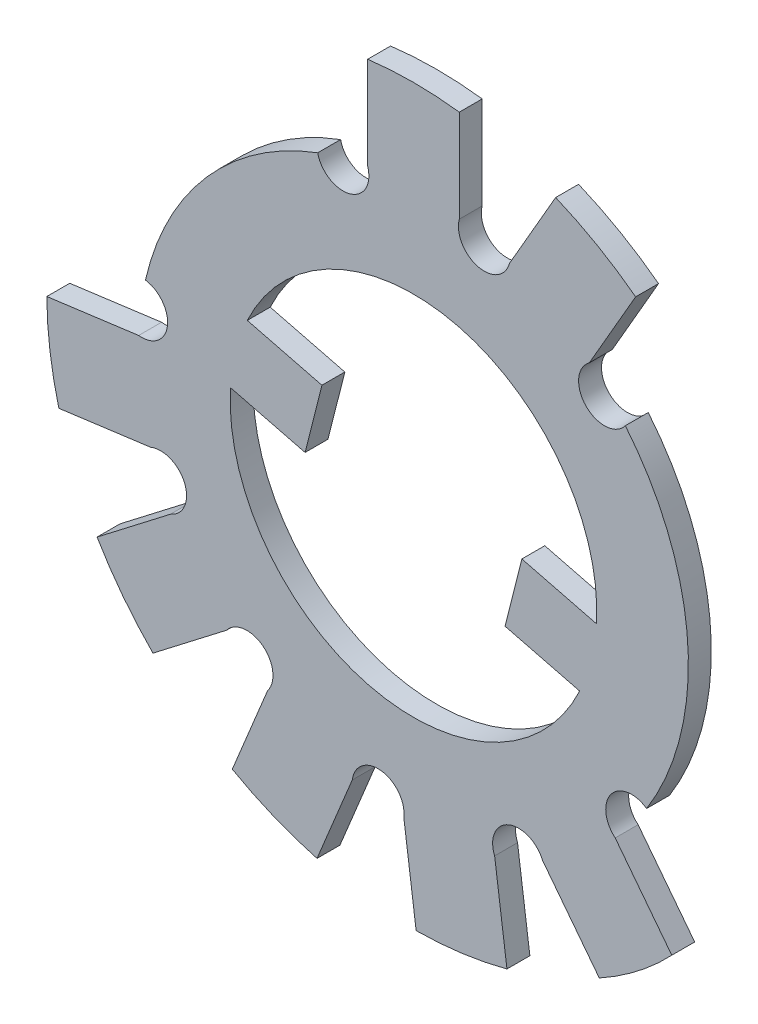
SolidWorks part; units mm, degrees
ref_plane "Face" through (0, 0, 0) normal (0, 0, 1) x (1, 0, 0)
ref_plane "Dessus" through (0, 0, 0) normal (0, 1, 0) x (1, 0, 0)
ref_plane "Droite" through (0, 0, 0) normal (1, 0, 0) x (0, 0, -1)
sketch "Esquisse1" plane through (0, 0, 0) normal (0, 0, 1) x (1, 0, 0)
  line L0 (0, 0) -> (0, 17.0651) construction
  line L1 (0, 0) -> (1.3955, 1.3955) construction
  line L2 (1.9991, 15.8746) -> (1.9991, 11.8301)
  line L3 (0, 0) -> (12.3609, 21.4097) construction
  line L4 (-1.9991, 11.8323) -> (-1.9991, 15.8746)
  line L5 (4.1862, 11.2489) -> (6.2054, 14.7508)
  line L6 (9.6952, 12.7421) -> (7.6749, 9.2384)
  line L7 (-11.4682, -3.5253) -> (-15.4754, -4.057)
  line L8 (-16.0013, -0.0935) -> (-11.992, 0.4385)
  line L9 (-13.8069, -8.0883) -> (-10.6019, -5.6214)
  line L10 (-8.1649, -8.7911) -> (-11.3682, -11.2567)
  line L11 (-7.9063, -13.9119) -> (-6.366, -10.1722)
  line L12 (-2.6699, -11.697) -> (-4.2094, -15.4347)
  line L13 (0.1166, -16.0012) -> (-0.4212, -11.9926)
  line L14 (3.5418, -11.4632) -> (4.0793, -15.4696)
  line L15 (8.1082, -13.7953) -> (5.6366, -10.5938)
  line L16 (8.8028, -8.1523) -> (11.273, -11.352)
  line L17 (7.9862, -0.4691) -> (4.7303, 0.3529)
  line L18 (0.025, -0.0227) -> (9.7847, -12.6956) construction
  line L19 (-0.0128, -0.0017) -> (-15.8627, -2.0918) construction
  line L20 (3.9959, -2.5559) -> (7.2519, -3.3778)
  line L21 (-7.2519, 3.3778) -> (-3.9959, 2.5559)
  line L22 (-3.9959, 2.5559) -> (-4.7303, -0.3529)
  line L23 (-4.7303, -0.3529) -> (-7.9862, 0.4691)
  line L24 (4.7303, 0.3529) -> (3.9959, -2.5559)
  arc A0 (-4.1799, 11.2485) -> (-11.6971, 2.679) centre (0, 0) ccw
  arc A1 (7.9862, -0.4691) -> (-7.2519, 3.3778) centre (0, 0) ccw
  arc A2 (1.9991, 15.8746) -> (-1.9991, 15.8746) centre (0, 0) ccw
  arc A3 (9.6952, 12.7421) -> (6.2054, 14.7508) centre (0.025, -0.0227) ccw
  arc A4 (-16.0013, -0.0935) -> (-15.4754, -4.057) centre (-0.0017, 0.0128) ccw
  arc A5 (-13.8069, -8.0883) -> (-11.3682, -11.2567) centre (-0.0079, 0.0102) ccw
  arc A6 (-7.9063, -13.9119) -> (-4.2094, -15.4347) centre (-0.012, 0.0049) ccw
  arc A7 (0.1166, -16.0012) -> (4.0793, -15.4696) centre (-0.0128, -0.0017) ccw
  arc A8 (8.1082, -13.7953) -> (11.273, -11.352) centre (1.812, -2.3682) ccw
  arc A9 (-11.992, 0.4385) -> (-11.6971, 2.679) centre (-11.8583, 1.5605) ccw
  arc A10 (8.8028, -8.1523) -> (10.1747, -6.358) centre (9.52, -7.2791) cw
  arc A11 (-1.9991, 11.8323) -> (-4.1799, 11.2485) centre (-3.0759, 11.4895) cw
  arc A12 (10.1747, -6.358) -> (9.2456, 7.6464) centre (0, 0) ccw
  arc A13 (-7.9862, 0.4691) -> (7.2519, -3.3778) centre (0, 0) ccw
  arc A14 (1.9991, 11.8301) -> (4.1862, 11.2489) centre (3.0927, 11.5395) ccw
  arc A15 (-11.4682, -3.5253) -> (-10.6019, -5.6214) centre (-11.0351, -4.5733) cw
  arc A16 (-8.1649, -8.7911) -> (-6.366, -10.1722) centre (-7.2654, -9.4816) cw
  arc A17 (-2.6699, -11.697) -> (-0.4212, -11.9926) centre (-1.5455, -11.8448) cw
  arc A18 (3.5418, -11.4632) -> (5.6366, -10.5938) centre (4.5892, -11.0285) cw
  arc A19 (9.2456, 7.6464) -> (7.6749, 9.2384) centre (8.3374, 8.3212) cw
  dimension "D1" = 24
  dimension "D2" = 32
  dimension "D4" = 1.13
  dimension "D5" = 1.13
  dimension "D6" = 1.13
  dimension "D7" = 11.9978
  dimension "D8" = 1.134
  dimension "D9" = 1.134
  dimension "D10" = 1.134
  dimension "D11" = 1.1315
  dimension "D3" = 30
extrude "Extrusion1" add sketch "Esquisse1" along normal blind 1
